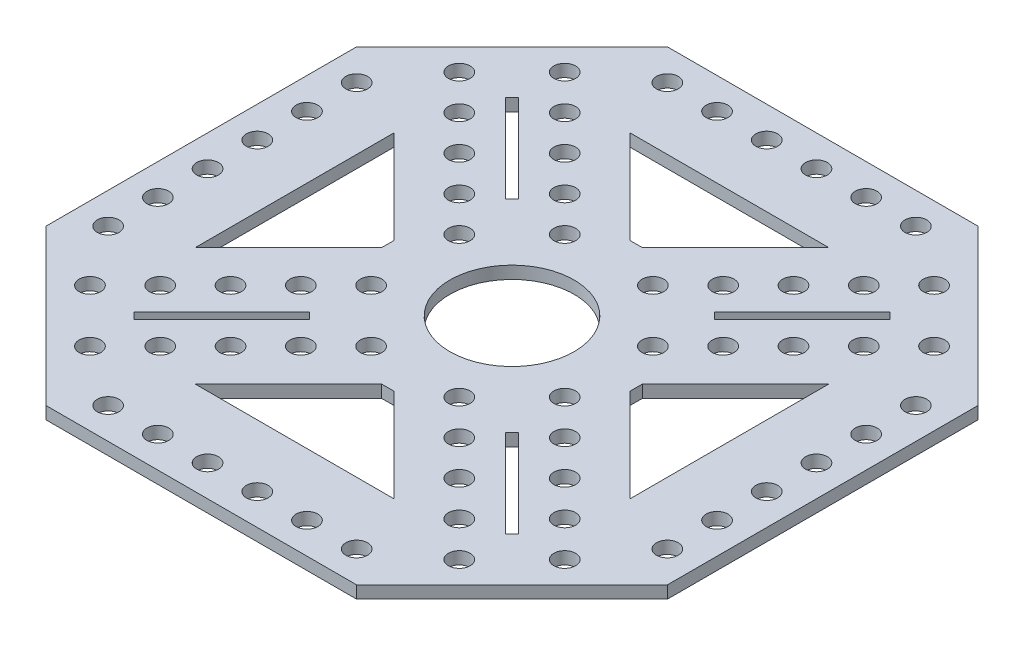
SolidWorks part; units mm, degrees
ref_plane "Front Plane" through (0, 0, 0) normal (0, 0, 1) x (1, 0, 0)
ref_plane "Top Plane" through (0, 0, 0) normal (0, 1, 0) x (1, 0, 0)
ref_plane "Right Plane" through (0, 0, 0) normal (1, 0, 0) x (0, 0, -1)
sketch "Sketch1" plane through (0, 0, 0) normal (0, 1, 0) x (1, 0, 0)
  line L0 (-25, 50) -> (25, 50)
  line L1 (25, 50) -> (50, 25)
  line L2 (50, 25) -> (50, -25)
  line L3 (50, -25) -> (25, -50)
  line L4 (25, -50) -> (-25, -50)
  line L5 (-25, -50) -> (-50, -25)
  line L6 (-50, -25) -> (-50, 25)
  line L7 (-50, 25) -> (-25, 50)
  line L8 (0, 0) -> (0, 50) construction
  line L9 (0, 0) -> (50, 0) construction
  line L10 (-50, 0) -> (0, 0) construction
  line L11 (0, 0) -> (0, -50) construction
  dimension "D1" = 50
  dimension "D2" = 50
  dimension "D3" = 50
  dimension "D4" = 50
  dimension "D5" = 50
  dimension "D6" = 50
  dimension "D7" = 50
extrude "Boss-Extrude1" add sketch "Sketch1" along normal blind 2
sketch "Sketch3" plane through (0, 2, 0) normal (0, 1, 0) x (1, 0, 0)
  circle A0 centre (0, 0) radius 10
  dimension "D1" = 20
extrude "Cut-Extrude2" cut sketch "Sketch3" against normal blind 2
sketch "Sketch2" plane through (0, 2, 0) normal (0, 1, 0) x (1, 0, 0)
  line L0 (-50, 25) -> (-50, -25) construction
  circle A0 centre (-45, 20) radius 1.75
  circle A1 centre (-45, 12) radius 1.75
  circle A2 centre (-45, 4) radius 1.75
  circle A3 centre (-45, -4) radius 1.75
  circle A4 centre (-45, -12) radius 1.75
  circle A5 centre (-45, -20) radius 1.75
  dimension "D2" = 3.5
  dimension "D1" = 5
  dimension "D3" = 5
  dimension "D4" = 6
extrude "Cut-Extrude1" cut sketch "Sketch2" against normal blind 2
sketch "Sketch4" plane through (0, 2, 0) normal (0, 1, 0) x (1, 0, 0)
  line L0 (-30.9593, 29.8986) -> (-16.8171, 15.7565)
  line L1 (-30.9593, 29.8986) -> (-29.8986, 30.9593)
  line L2 (-16.8171, 15.7565) -> (-15.7565, 16.8171)
  line L3 (-29.8986, 30.9593) -> (-15.7565, 16.8171)
  line L4 (-30.9593, 29.8986) -> (-15.7565, 16.8171) construction
  line L5 (-16.8171, 15.7565) -> (-29.8986, 30.9593) construction
  line L6 (-23.3579, 23.3579) -> (-37.5, 37.5) construction
  line L7 (-25, 50) -> (-50, 25) construction
  line L8 (-35, 16) -> (-20, 1)
  line L9 (-20, 1) -> (-20, -1)
  line L10 (-20, -1) -> (-35, -16)
  line L11 (-35, -16) -> (-35, 16)
  line L12 (-20, 0) -> (0, 0) construction
  circle A0 centre (-29.7218, 38.2071) radius 1.75
  circle A1 centre (-24.065, 32.5503) radius 1.75
  circle A2 centre (-18.4081, 26.8934) radius 1.75
  circle A3 centre (-12.7513, 21.2365) radius 1.75
  circle A4 centre (-7.0944, 15.5797) radius 1.75
  circle A5 centre (-15.5797, 7.0944) radius 1.75
  circle A6 centre (-21.2365, 12.7513) radius 1.75
  circle A7 centre (-26.8934, 18.4081) radius 1.75
  circle A8 centre (-32.5503, 24.065) radius 1.75
  circle A9 centre (-38.2071, 29.7218) radius 1.75
  point P1 (-23.3579, 23.3579)
  dimension "D7" = 3.5
  dimension "D1" = 20
  dimension "D2" = 20
  dimension "D3" = 1.5
  dimension "D4" = 20
  dimension "D5" = 35
  dimension "D6" = 2
  dimension "D8" = 5
  dimension "D9" = 6
  dimension "D10" = 5
extrude "Cut-Extrude3" cut sketch "Sketch4" against normal blind 2
pattern_circular "CirPattern1" count 4 every 90 about axis through (0, 0, 0) along (0, 1, 0) of "Cut-Extrude1", "Cut-Extrude3"
